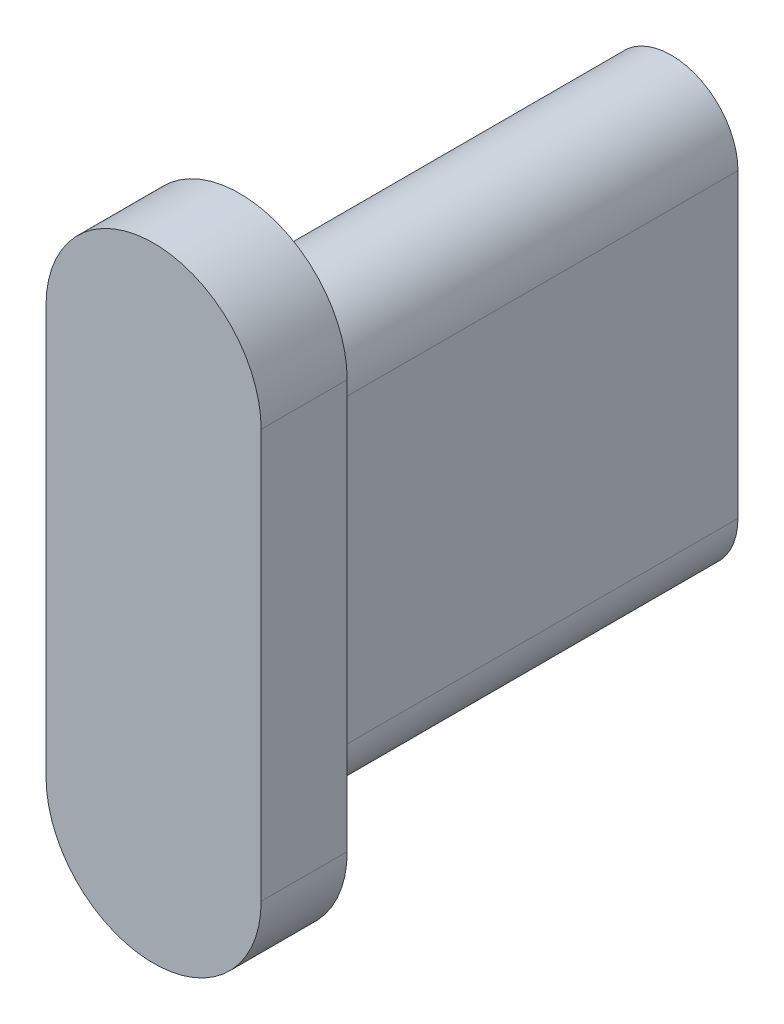
SolidWorks part; units mm, degrees
ref_plane "Plan de face" through (0, 0, 0) normal (0, 0, 1) x (1, 0, 0)
ref_plane "Plan de dessus" through (0, 0, 0) normal (0, 1, 0) x (1, 0, 0)
ref_plane "Plan de droite" through (0, 0, 0) normal (1, 0, 0) x (0, 0, -1)
sketch "Esquisse1" plane through (0, 0, 0) normal (0, 0, 1) x (1, 0, 0)
  line L2 (-1.5171, 11.0177) -> (-1.5171, 4.0177)
  line L3 (1.5829, 4.0177) -> (1.5829, 11.0177)
  line L4 (-0.5171, 11.0177) -> (-0.5171, 4.0177)
  line L5 (0.5829, 4.0177) -> (0.5829, 11.0177)
  line L6 (-0.5171, 11.0177) -> (-0.5171, 4.0177)
  line L7 (0.5829, 4.0177) -> (0.5829, 11.0177)
  arc A2 (-1.5171, 4.0177) -> (1.5829, 4.0177) centre (0.0329, 4.0177) ccw
  arc A3 (1.5829, 11.0177) -> (-1.5171, 11.0177) centre (0.0329, 11.0177) ccw
  arc A4 (0.5829, 11.0177) -> (-0.5171, 11.0177) centre (0.0329, 11.0177) ccw
  arc A5 (-0.5171, 4.0177) -> (0.5829, 4.0177) centre (0.0329, 4.0177) ccw
  arc A6 (0.5829, 11.0177) -> (-0.5171, 11.0177) centre (0.0329, 11.0177) ccw
  arc A7 (-0.5171, 4.0177) -> (0.5829, 4.0177) centre (0.0329, 4.0177) ccw
  dimension "D1" = 0.05
  dimension "D2" = 1
extrude "Boss.-Extru.3" add sketch "Esquisse1" against normal blind 10
sketch "Esquisse3" plane through (0, 0, 0) normal (0, 0, 1) x (1, 0, 0)
  line L2 (0, 2.7677) -> (0, 12.2677) construction
  line L3 (-2.5, 2.7677) -> (-2.5, 12.2677)
  line L4 (2.5, 2.7677) -> (2.5, 12.2677)
  line L5 (2.5, 7.5177) -> (-2.5, 7.5177) construction
  line L7 (0.5829, 4.0177) -> (0.5829, 11.0177) construction
  arc A2 (-2.5, 2.7677) -> (2.5, 2.7677) centre (0, 2.7677) ccw
  arc A3 (2.5, 12.2677) -> (-2.5, 12.2677) centre (0, 12.2677) ccw
  point P2 (0, 7.5177)
  point P14 (0.5829, 7.5177)
  dimension "D1" = 5
  dimension "D2" = 9.5
extrude "Boss.-Extru.4" add sketch "Esquisse3" along normal blind 2
